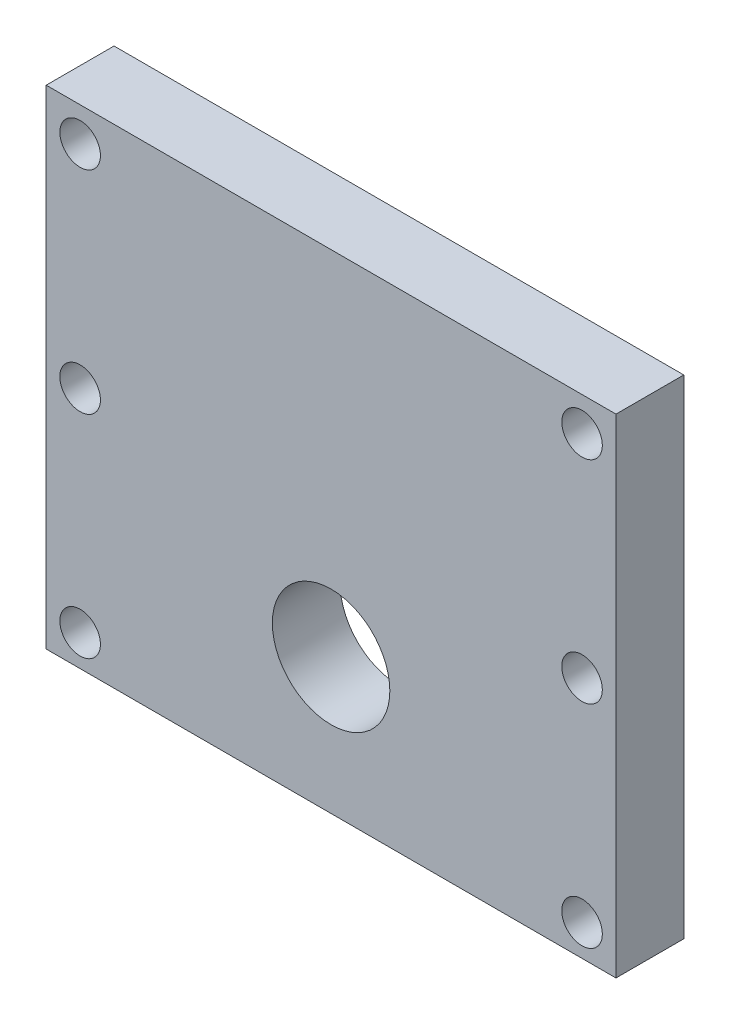
SolidWorks part; units mm, degrees
material "6061-T6 (SS)"
ref_plane "Front Plane" through (0, 0, 0) normal (0, 0, 1) x (1, 0, 0)
ref_plane "Top Plane" through (0, 0, 0) normal (0, 1, 0) x (1, 0, 0)
ref_plane "Right Plane" through (0, 0, 0) normal (1, 0, 0) x (0, 0, -1)
sketch "Sketch1" plane through (0, 0, 0) normal (0, 0, 1) x (1, 0, 0)
  line L1 (0, 0) -> (53.34, 0)
  line L2 (0, 0) -> (0, 45.72)
  line L3 (0, 45.72) -> (53.34, 45.72)
  line L4 (53.34, 0) -> (53.34, 45.72)
  dimension "D1" = 53.34
  dimension "D2" = 45.72
extrude "Boss-Extrude1" add sketch "Sketch1" along normal blind 6.35
sketch "Sketch2" plane through (0, 0, 6.35) normal (0, 0, 1) x (1, 0, 0)
  line L0 (53.34, 45.72) -> (0, 45.72) construction
  circle A0 centre (26.67, 12.7) radius 5.5
  point P4 (26.67, 45.72)
  dimension "D1" = 11
  dimension "D3" = 33.02
  dimension "D2" = 0
extrude "Cut-Extrude1" cut sketch "Sketch2" against normal through all both and the other way through all
hole_wizard "#6 Clearance Hole1" positions "Sketch5" profile "Sketch4" hole size "#6" standard "ANSI Inch" end condition up to next
sketch "Sketch5" plane through (0, 0, 6.35) normal (0, 0, 1) x (1, 0, 0)
  line L0 (0, 45.72) -> (0, 0) construction
  line L2 (53.34, 45.72) -> (0, 45.72) construction
  line L3 (53.34, 0) -> (53.34, 45.72) construction
  point P0 (3.175, 42.545)
  point P10 (50.165, 42.545)
  point P11 (50.165, 22.733)
  point P12 (50.165, 2.921)
  point P13 (3.175, 22.733)
  point P14 (3.175, 2.921)
  dimension "D3" = 3.175
  dimension "D4" = 3.175
  dimension "D5" = 3.175
  dimension "D1" = 2
  dimension "D2" = 3
sketch "Sketch4" plane through (3.175, 42.545, 6.35) normal (1, 0, 0) x (0, -1, 0)
  line L0 (0, 0) -> (0, 6.35)
  line L1 (0, 6.35) -> (1.8986, 6.35)
  line L2 (1.8986, 6.35) -> (1.8986, 0)
  line L5 (1.8986, 0) -> (0, 0)
  line L11 (0, -6.35) -> (0, 107.95) construction
  dimension "Thru Hole Dia." = 3.7973
  dimension "Thru Hole Depth" = 6.35
